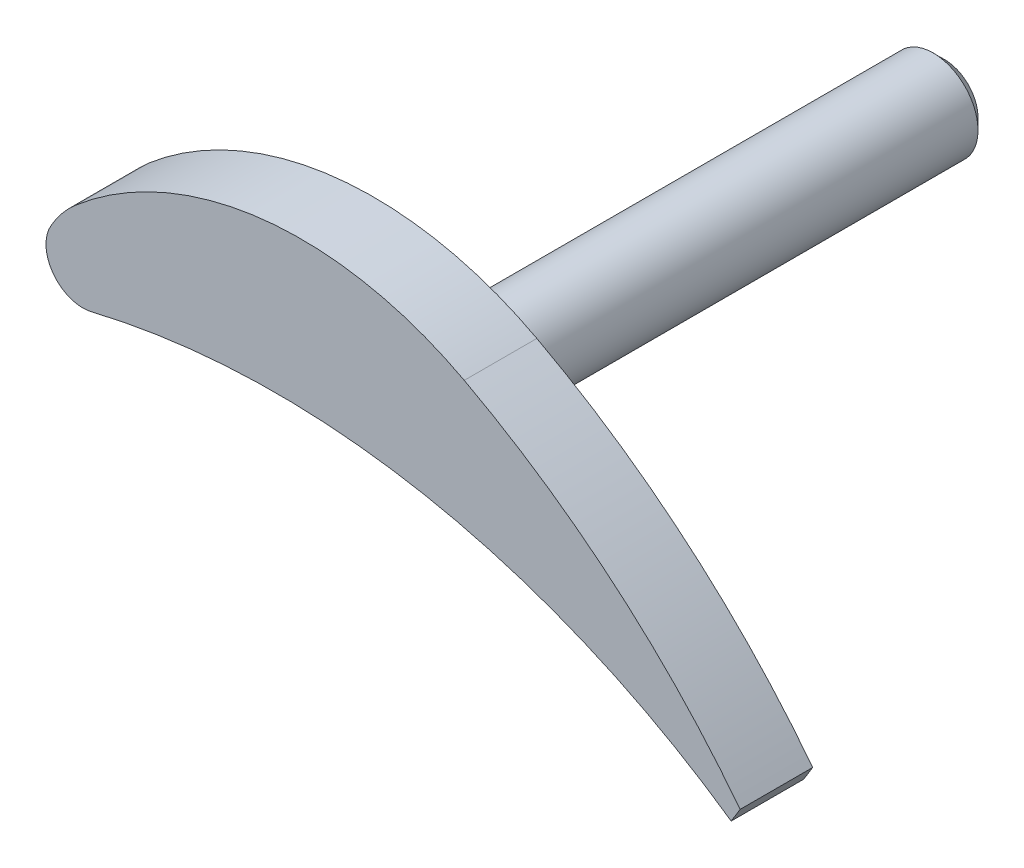
SolidWorks part; units mm, degrees
material "Brass"
ref_plane "Front Plane" through (0, 0, 0) normal (0, 0, 1) x (1, 0, 0)
ref_plane "Top Plane" through (0, 0, 0) normal (0, 1, 0) x (1, 0, 0)
ref_plane "Right Plane" through (0, 0, 0) normal (1, 0, 0) x (0, 0, -1)
sketch "Sketch1" plane through (0, 0, 0) normal (0, 0, 1) x (1, 0, 0)
  line L0 (29, 70.4036) -> (29, -82.4591) construction
  line L1 (28.1969, -18.3213) -> (29, -17.0106)
  arc A0 (-29.0918, -7.4659) -> (28.1969, -18.3213) centre (-12.5, -76.5) cw
  arc A1 (29, -17.0106) -> (4.2947, 3.9095) centre (-32, -64) ccw
  arc A2 (-32.7507, -2.6601) -> (-30.5155, 0.0861) centre (-24, -7.5) cw
  arc A3 (-32.7507, -2.6601) -> (-29.0918, -7.4659) centre (-29.863, -4.2572) ccw
  arc A4 (-30.5155, 0.0861) -> (4.2947, 3.9095) centre (-10.3174, -23.4307) cw
  dimension "D1" = 71
  dimension "D4" = 77
  dimension "D7" = 10
  dimension "D12" = 3.3
  dimension "D13" = 31
  dimension "D2" = 76.5
  dimension "D3" = 12.5
  dimension "D5" = 32
  dimension "D6" = 64
  dimension "D8" = 7.5
  dimension "D9" = 24
  dimension "D10" = 29
  dimension "D11" = 31.5
extrude "Boss-Extrude1" add sketch "Sketch1" along normal blind 6.5
sketch "Sketch2" plane through (0, 0, 0) normal (0, 0, -1) x (-1, 0, 0)
  circle A0 centre (0, 0) radius 4
  dimension "D1" = 8
extrude "Boss-Extrude2" add sketch "Sketch2" along normal blind 40.8
chamfer "Chamfer1" distance 1 angle 45 1 edges at (-4, 0, -40.8)
